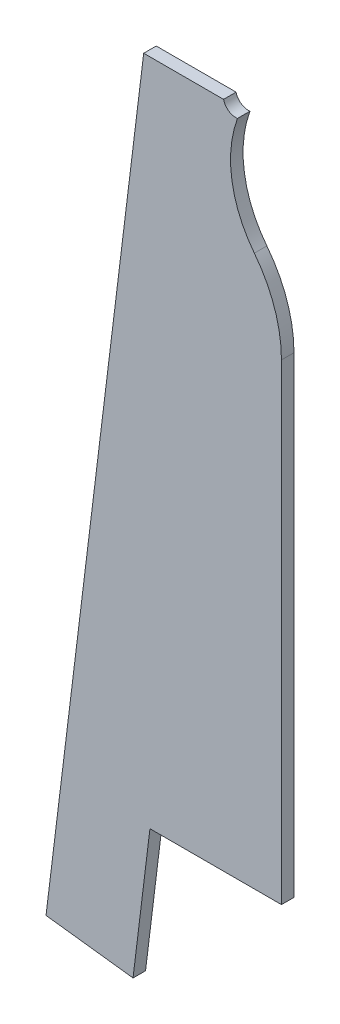
SolidWorks part; units mm, degrees
ref_plane "Front Plane" through (0, 0, 0) normal (0, 0, 1) x (1, 0, 0)
ref_plane "Top Plane" through (0, 0, 0) normal (0, 1, 0) x (1, 0, 0)
ref_plane "Right Plane" through (0, 0, 0) normal (1, 0, 0) x (0, 0, -1)
sketch "Sketch1" plane through (0, 0, 0) normal (0, 0, 1) x (1, 0, 0)
  line L0 (20.5051, 25.8971) -> (-23.6135, 31.3142)
  line L1 (20.5051, 25.8971) -> (70.0328, 429.2678) construction
  line L2 (-23.6135, 31.3142) -> (25.9142, 434.6849)
  line L3 (95.7642, 95.7471) -> (29.0816, 95.7471)
  line L4 (65.8872, -89.4093) -> (336.2328, -89.4093) construction
  line L5 (291.7277, 345.7849) -> (-86.6189, 345.7849) construction
  line L6 (95.7642, 95.7471) -> (95.7642, 434.6849)
  line L7 (29.0816, 95.7471) -> (20.5051, 25.8971)
  line L11 (25.9142, 434.6849) -> (95.7642, 434.6849)
  point P4 (14.9986, 345.7849)
  dimension "D1" = 406.4
  dimension "D2" = 44.45
  dimension "D3" = 83
  dimension "D4" = 88.9
  dimension "D5" = 69.85
extrude "Boss-Extrude1" add sketch "Sketch1" along normal blind 6.35
sketch "Sketch2" plane through (0, 0, 6.35) normal (0, 0, 1) x (1, 0, 0)
  circle A0 centre (72.5949, 436.1354) radius 6.35
  dimension "D1" = 12.7
extrude "Cut-Extrude1" cut sketch "Sketch2" against normal blind 6.35
sketch "Sketch4" plane through (0, 0, 6.35) normal (0, 0, 1) x (1, 0, 0)
  line L0 (20.5051, 25.8971) -> (79.1489, 503.5123) construction
  line L1 (74.295, 431.9433) -> (82.0162, 440.3614)
  line L2 (82.0162, 440.3614) -> (105.9899, 438.1646)
  line L3 (95.7642, 334.936) -> (105.9899, 438.1646)
  arc A0 (74.295, 431.9433) -> (82.0162, 374.944) centre (127.0947, 410.073) ccw construction
  arc A1 (82.0162, 374.944) -> (95.7642, 334.936) centre (30.6767, 334.936) cw
  arc A2 (74.295, 431.9433) -> (82.0162, 374.944) centre (127.0947, 410.073) ccw
extrude "Cut-Extrude4" cut sketch "Sketch4" against normal blind 6.35
